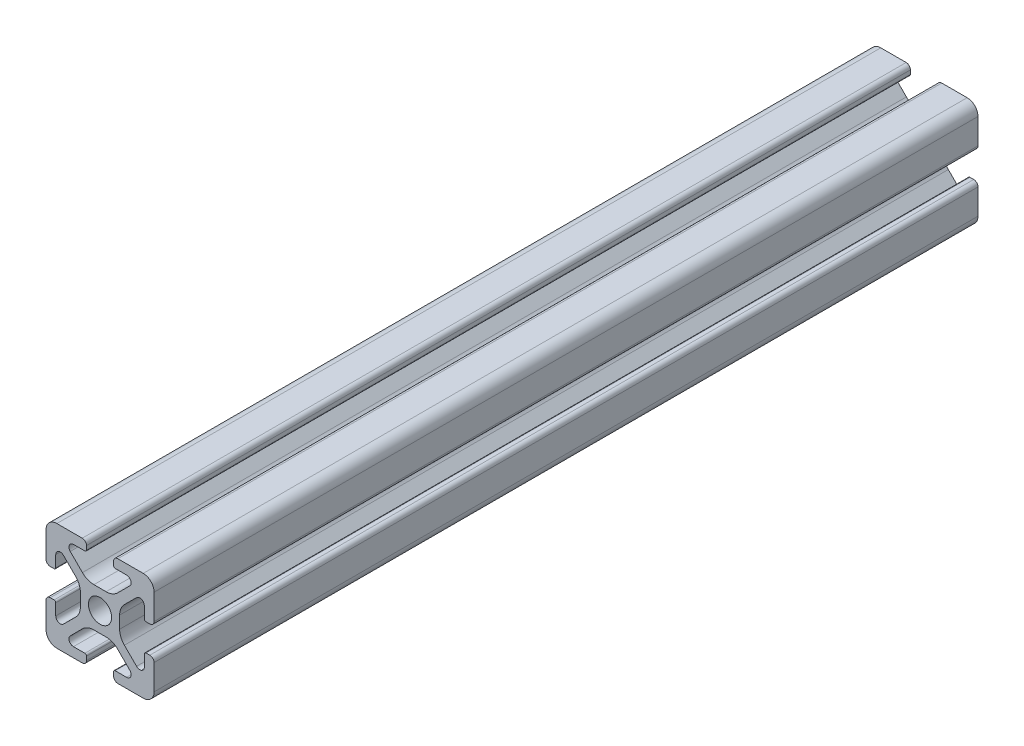
SolidWorks part; units mm, degrees
ref_plane "Front Plane" through (0, 0, 0) normal (0, 0, 1) x (1, 0, 0)
ref_plane "Top Plane" through (0, 0, 0) normal (0, 1, 0) x (1, 0, 0)
ref_plane "Right Plane" through (0, 0, 0) normal (1, 0, 0) x (0, 0, -1)
sketch "Sketch1" plane through (0, 0, 0) normal (0, 0, 1) x (1, 0, 0)
  line L2 (-9.9949, 7.9883) -> (-9.9949, 3.2893)
  line L3 (-7.9883, 9.9949) -> (-3.2893, 9.9949)
  line L4 (-2.5019, 9.2075) -> (-2.5019, 8.4963)
  line L5 (-2.8067, 8.1915) -> (-4.9149, 8.1915)
  line L6 (-5.5076, 6.7606) -> (-3.2528, 4.5058)
  line L7 (-6.7606, 5.5076) -> (-4.5058, 3.2528)
  line L8 (-8.1915, 4.9149) -> (-8.1915, 2.8067)
  line L9 (-8.4963, 2.5019) -> (-9.2075, 2.5019)
  line L11 (-1.1334, 3.6279) -> (1.1334, 3.6279)
  line L12 (-3.6279, 1.1334) -> (-3.6279, -1.1334)
  line L13 (8.4963, 2.5019) -> (9.2075, 2.5019)
  line L14 (8.1915, 4.9149) -> (8.1915, 2.8067)
  line L15 (9.9949, 7.9883) -> (9.9949, 3.2893)
  line L16 (7.9883, 9.9949) -> (3.2893, 9.9949)
  line L17 (2.5019, 9.2075) -> (2.5019, 8.4963)
  line L18 (2.8067, 8.1915) -> (4.9149, 8.1915)
  line L19 (3.6279, 1.1334) -> (3.6279, -1.1334)
  line L20 (5.5076, 6.7606) -> (3.2528, 4.5058)
  line L21 (6.7606, 5.5076) -> (4.5058, 3.2528)
  line L22 (-8.4963, -2.5019) -> (-9.2075, -2.5019)
  line L23 (-8.1915, -4.9149) -> (-8.1915, -2.8067)
  line L24 (-6.7606, -5.5076) -> (-4.5058, -3.2528)
  line L25 (-5.5076, -6.7606) -> (-3.2528, -4.5058)
  line L26 (-2.8067, -8.1915) -> (-4.9149, -8.1915)
  line L27 (-2.5019, -9.2075) -> (-2.5019, -8.4963)
  line L28 (-7.9883, -9.9949) -> (-3.2893, -9.9949)
  line L29 (-9.9949, -7.9883) -> (-9.9949, -3.2893)
  line L30 (9.9949, -7.9883) -> (9.9949, -3.2893)
  line L31 (7.9883, -9.9949) -> (3.2893, -9.9949)
  line L32 (2.5019, -9.2075) -> (2.5019, -8.4963)
  line L33 (2.8067, -8.1915) -> (4.9149, -8.1915)
  line L34 (5.5076, -6.7606) -> (3.2528, -4.5058)
  line L35 (6.7606, -5.5076) -> (4.5058, -3.2528)
  line L36 (8.1915, -4.9149) -> (8.1915, -2.8067)
  line L37 (8.4963, -2.5019) -> (9.2075, -2.5019)
  line L38 (-1.1334, -3.6279) -> (1.1334, -3.6279)
  circle A0 centre (0, 0) radius 2.1463
  arc A1 (-9.9949, 7.9883) -> (-7.9883, 9.9949) centre (-7.9883, 7.9883) cw
  arc A2 (-6.7606, 5.5076) -> (-8.1915, 4.9149) centre (-7.3533, 4.9149) ccw
  arc A3 (-4.9149, 8.1915) -> (-5.5076, 6.7606) centre (-4.9149, 7.3533) ccw
  arc A4 (-3.2893, 9.9949) -> (-2.5019, 9.2075) centre (-3.2893, 9.2075) cw
  arc A5 (-9.9949, 3.2893) -> (-9.2075, 2.5019) centre (-9.2075, 3.2893) ccw
  arc A6 (-8.1915, 2.8067) -> (-8.4963, 2.5019) centre (-8.4963, 2.8067) cw
  arc A7 (-2.5019, 8.4963) -> (-2.8067, 8.1915) centre (-2.8067, 8.4963) cw
  arc A8 (-1.1334, 3.6279) -> (-3.2528, 4.5058) centre (-1.1334, 6.6251) cw
  arc A9 (-3.6279, 1.1334) -> (-4.5058, 3.2528) centre (-6.6251, 1.1334) ccw
  arc A10 (8.1915, 2.8067) -> (8.4963, 2.5019) centre (8.4963, 2.8067) ccw
  arc A11 (9.9949, 3.2893) -> (9.2075, 2.5019) centre (9.2075, 3.2893) cw
  arc A12 (9.9949, 7.9883) -> (7.9883, 9.9949) centre (7.9883, 7.9883) ccw
  arc A13 (3.2893, 9.9949) -> (2.5019, 9.2075) centre (3.2893, 9.2075) ccw
  arc A14 (2.5019, 8.4963) -> (2.8067, 8.1915) centre (2.8067, 8.4963) ccw
  arc A15 (1.1334, 3.6279) -> (3.2528, 4.5058) centre (1.1334, 6.6251) ccw
  arc A16 (3.6279, 1.1334) -> (4.5058, 3.2528) centre (6.6251, 1.1334) cw
  arc A17 (6.7606, 5.5076) -> (8.1915, 4.9149) centre (7.3533, 4.9149) cw
  arc A18 (4.9149, 8.1915) -> (5.5076, 6.7606) centre (4.9149, 7.3533) cw
  arc A19 (-3.6279, -1.1334) -> (-4.5058, -3.2528) centre (-6.6251, -1.1334) cw
  arc A20 (-1.1334, -3.6279) -> (-3.2528, -4.5058) centre (-1.1334, -6.6251) ccw
  arc A21 (-2.5019, -8.4963) -> (-2.8067, -8.1915) centre (-2.8067, -8.4963) ccw
  arc A22 (-8.1915, -2.8067) -> (-8.4963, -2.5019) centre (-8.4963, -2.8067) ccw
  arc A23 (-9.9949, -3.2893) -> (-9.2075, -2.5019) centre (-9.2075, -3.2893) cw
  arc A24 (-3.2893, -9.9949) -> (-2.5019, -9.2075) centre (-3.2893, -9.2075) ccw
  arc A25 (-4.9149, -8.1915) -> (-5.5076, -6.7606) centre (-4.9149, -7.3533) cw
  arc A26 (-6.7606, -5.5076) -> (-8.1915, -4.9149) centre (-7.3533, -4.9149) cw
  arc A27 (-9.9949, -7.9883) -> (-7.9883, -9.9949) centre (-7.9883, -7.9883) ccw
  arc A28 (9.9949, -7.9883) -> (7.9883, -9.9949) centre (7.9883, -7.9883) cw
  arc A29 (6.7606, -5.5076) -> (8.1915, -4.9149) centre (7.3533, -4.9149) ccw
  arc A30 (4.9149, -8.1915) -> (5.5076, -6.7606) centre (4.9149, -7.3533) ccw
  arc A31 (3.2893, -9.9949) -> (2.5019, -9.2075) centre (3.2893, -9.2075) cw
  arc A32 (9.9949, -3.2893) -> (9.2075, -2.5019) centre (9.2075, -3.2893) ccw
  arc A33 (8.1915, -2.8067) -> (8.4963, -2.5019) centre (8.4963, -2.8067) cw
  arc A34 (2.5019, -8.4963) -> (2.8067, -8.1915) centre (2.8067, -8.4963) cw
  arc A35 (1.1334, -3.6279) -> (3.2528, -4.5058) centre (1.1334, -6.6251) cw
  arc A36 (3.6279, -1.1334) -> (4.5058, -3.2528) centre (6.6251, -1.1334) ccw
extrude "Boss-Extrude1" add sketch "Sketch1" along normal mid plane 304.8
sketch "Sketch2" plane through (0, 0, 152.4) normal (0, 0, 1) x (1, 0, 0)
  line L1 (-14.8385, 12.1395) -> (15.2996, 12.1395)
  line L2 (-14.8385, 12.1395) -> (-14.8385, -13.8304)
  line L3 (-14.8385, -13.8304) -> (15.2996, -13.8304)
  line L4 (15.2996, 12.1395) -> (15.2996, -13.8304)
extrude "Cut-Extrude1" cut sketch "Sketch2" against normal blind 152.4
